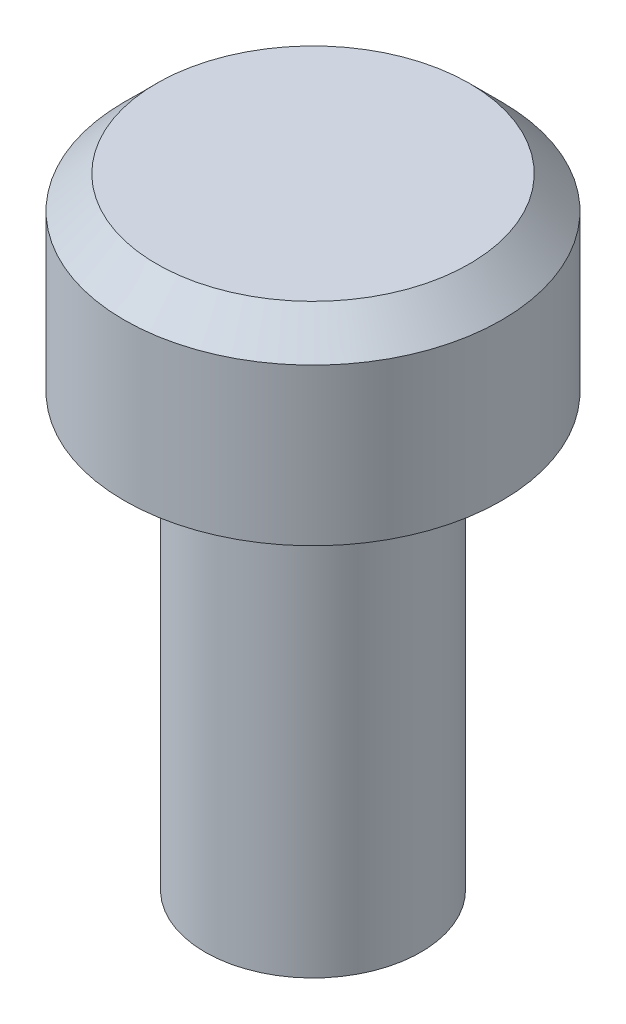
SolidWorks part; units mm, degrees
ref_plane "Спереди" through (0, 0, 0) normal (0, 0, 1) x (1, 0, 0)
ref_plane "Сверху" through (0, 0, 0) normal (0, 1, 0) x (1, 0, 0)
ref_plane "Справа" through (0, 0, 0) normal (1, 0, 0) x (0, 0, -1)
sketch "Sketch1" plane through (0, 0, 0) normal (0, 0, 1) x (1, 0, 0)
  line L0 (0, -4.6027) -> (0, 8.1773) construction
  line L1 (-1.45, 1.75) -> (-1.75, 1.45)
  line L3 (0, 1.75) -> (0, -4)
  line L4 (0, -4) -> (-1, -4)
  line L5 (-1, 0) -> (-1, -4)
  line L6 (-1, 0) -> (-1.75, 0)
  line L8 (0, 1.75) -> (-1.45, 1.75)
  line L9 (-1.75, 0) -> (-1.75, 1.45)
  point P7 (-1.75, 1.75)
  dimension "D1" = 2
  dimension "D2" = 3.5
  dimension "D3" = 1.75
  dimension "D4" = 5.75
revolve "Revolve1" add sketch "Sketch1" angle 360 about L0
